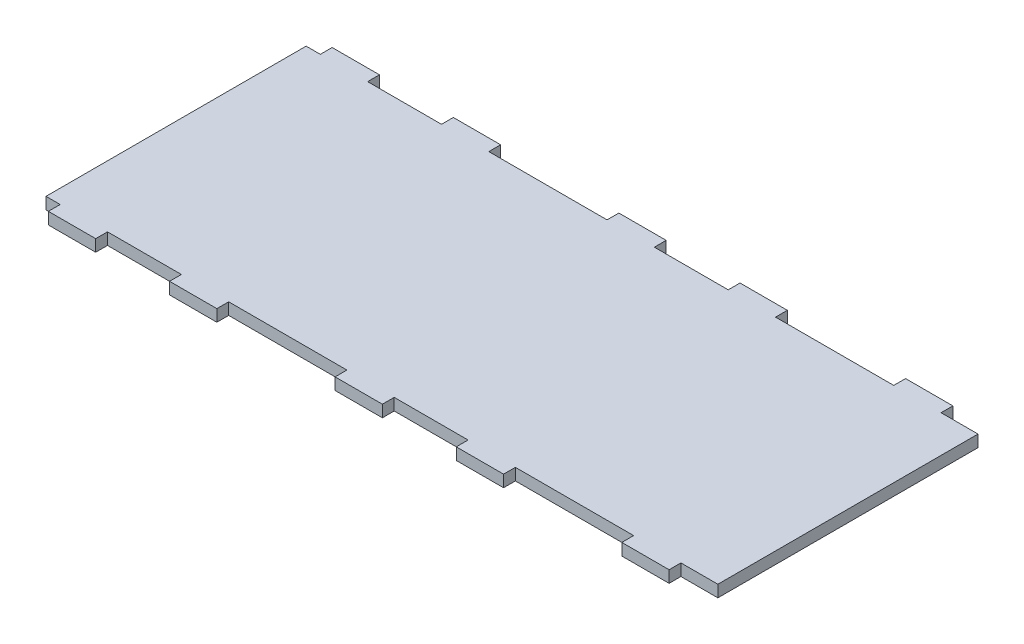
SolidWorks part; units mm, degrees
material "Cedar"
ref_plane "Front Plane" through (0, 0, 0) normal (0, 0, 1) x (1, 0, 0)
ref_plane "Top Plane" through (0, 0, 0) normal (0, 1, 0) x (1, 0, 0)
ref_plane "Right Plane" through (0, 0, 0) normal (1, 0, 0) x (0, 0, -1)
sketch "Sketch1" plane through (0, 0, 0) normal (0, 1, 0) x (1, 0, 0)
  line L1 (-360.8183, 76.2) -> (360.8183, 76.2)
  line L2 (-360.8183, 76.2) -> (-360.8183, -76.2)
  line L3 (-360.8183, -76.2) -> (360.8183, -76.2)
  line L4 (360.8183, 76.2) -> (360.8183, -76.2)
  line L5 (-360.8183, 76.2) -> (360.8183, -76.2) construction
  line L6 (-360.8183, -76.2) -> (360.8183, 76.2) construction
  point P0 (0, 0)
  dimension "D1" = 721.6366
  dimension "D2" = 152.4
extrude "Boss-Extrude1" add sketch "Sketch1" along normal blind 6.35
sketch "Sketch2" plane through (0, 6.35, 0) normal (0, 1, 0) x (1, 0, 0)
  line L0 (0, -76.2) -> (0, -69.85) construction
  line L1 (-32.5397, -69.85) -> (32.5397, -69.85) construction
  line L2 (-45.2397, -69.85) -> (-19.8397, -69.85) construction
  line L3 (-45.2397, -69.85) -> (-45.2397, -76.2) construction
  line L4 (-45.2397, -76.2) -> (-19.8397, -76.2) construction
  line L5 (-19.8397, -69.85) -> (-19.8397, -76.2)
  line L6 (-45.2397, -69.85) -> (-19.8397, -76.2) construction
  line L7 (-45.2397, -76.2) -> (-19.8397, -69.85) construction
  line L8 (-360.8183, -76.2) -> (360.8183, -76.2) construction
  line L9 (-19.8397, -69.85) -> (19.8397, -69.85)
  line L10 (19.8397, -69.85) -> (45.2397, -69.85) construction
  line L11 (19.8397, -69.85) -> (19.8397, -76.2)
  line L12 (19.8397, -76.2) -> (45.2397, -76.2) construction
  line L13 (45.2397, -69.85) -> (45.2397, -76.2) construction
  line L14 (19.8397, -69.85) -> (45.2397, -76.2) construction
  line L15 (19.8397, -76.2) -> (45.2397, -69.85) construction
  line L16 (19.8397, -76.2) -> (-19.8397, -76.2)
  line L17 (-45.2397, -76.2) -> (-45.2397, -69.85)
  line L18 (-45.2397, -69.85) -> (-76.9897, -69.85)
  line L19 (-76.9897, -69.85) -> (-76.9897, -76.2)
  line L20 (-76.9897, -76.2) -> (-45.2397, -76.2)
  line L21 (45.2397, -69.85) -> (76.9897, -69.85)
  line L22 (76.9897, -69.85) -> (76.9897, -76.2)
  line L23 (76.9897, -76.2) -> (45.2397, -76.2)
  line L24 (45.2397, -76.2) -> (45.2397, -69.85)
  point P5 (0, -69.85)
  point P6 (-32.5397, -73.025)
  point P11 (-32.5397, -69.85)
  point P17 (32.5397, -73.025)
  point P24 (32.5397, -69.85)
  dimension "D1" = 39.6793
  dimension "D2" = 25.4
  dimension "D3" = 6.35
  dimension "D4" = 76.9897
  dimension "D5" = 25.4
  dimension "D6" = 6.35
  dimension "D7" = 76.9897
extrude "Cut-Extrude1" cut sketch "Sketch2" against normal through all
pattern_linear "LPattern1" count 3 spacing 153.9793 along (1, 0, 0) count 3 spacing 153.9793 along (-1, 0, 0) of "Cut-Extrude1"
mirror "Mirror1" about plane through (0, 0, 0) normal (0, 0, 1) of "LPattern1", "Cut-Extrude1"
sketch "Sketch4" plane through (0, 6.35, 0) normal (0, 1, 0) x (1, 0, 0)
  line L0 (0, 76.2) -> (0, -76.2)
  line L1 (0, -76.2) -> (360.8183, -76.2)
  line L2 (360.8183, -76.2) -> (360.8183, 76.2)
  line L3 (360.8183, 76.2) -> (0, 76.2)
extrude "Cut-Extrude2" cut sketch "Sketch4" against normal through all
